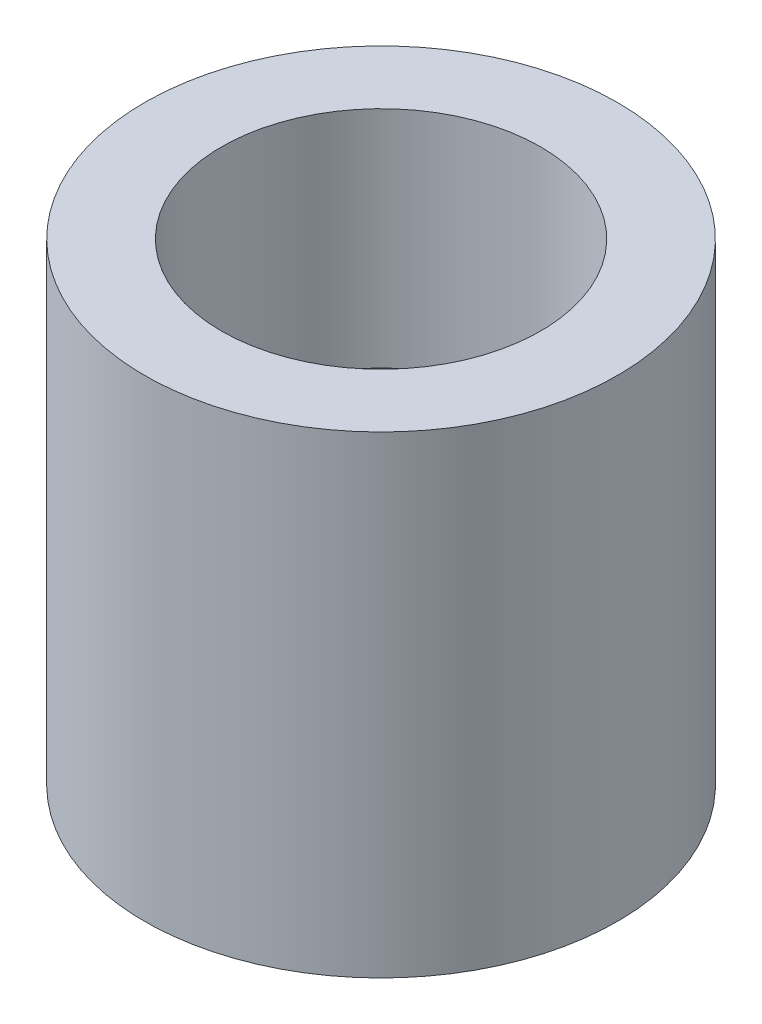
SolidWorks part; units mm, degrees
ref_plane "Спереди" through (0, 0, 0) normal (0, 0, 1) x (1, 0, 0)
ref_plane "Сверху" through (0, 0, 0) normal (0, 1, 0) x (1, 0, 0)
ref_plane "Справа" through (0, 0, 0) normal (1, 0, 0) x (0, 0, -1)
sketch "Эскиз1" plane through (0, 0, 0) normal (0, 0, 1) x (1, 0, 0)
  line L0 (7.25, 0) -> (10, 0)
  line L1 (10, 0) -> (10, 20)
  line L4 (6.75, 20) -> (6.75, 10.5)
  line L5 (6.75, 10.5) -> (7.25, 10.5)
  line L6 (7.25, 10.5) -> (7.25, 0)
  line L7 (6.75, 20) -> (10, 20)
  line L8 (0, -6.7103) -> (0, 28.5005) construction
  point P3 (0, 0)
  point P10 (0, 0)
  point P11 (0, 0)
  point P12 (0, 0)
  point P13 (0, 0)
  point P14 (0, 0)
  point P15 (0, 0)
  point P16 (0, 0)
  point P17 (0, 0)
  point P18 (0, 0)
revolve "Повернуть1" add sketch "Эскиз1" angle 360 about L8
